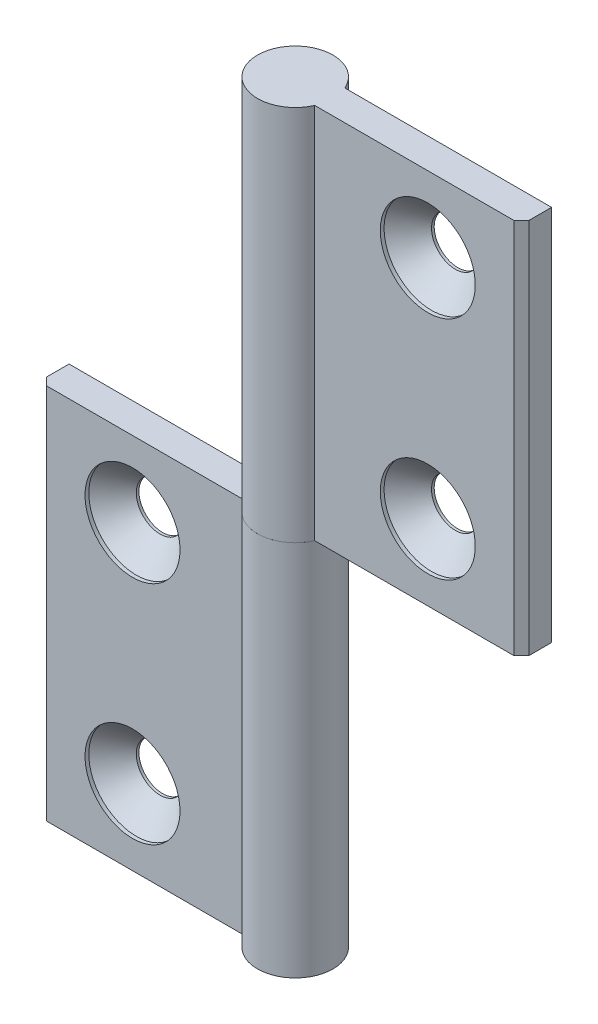
SolidWorks part; units mm, degrees
material "Алюминиевый сплав"
ref_plane "Спереди" through (0, 0, 0) normal (0, 0, 1) x (1, 0, 0)
ref_plane "Сверху" through (0, 0, 0) normal (0, 1, 0) x (1, 0, 0)
ref_plane "Справа" through (0, 0, 0) normal (1, 0, 0) x (0, 0, -1)
sketch "Эскиз1" plane through (0, 0, 0) normal (0, 1, 0) x (1, 0, 0)
  line L0 (-4.5826, 2) -> (-32, 2)
  line L1 (-32, 2) -> (-32, -1)
  line L2 (-32, -1) -> (-31, -2)
  line L3 (-31, -2) -> (-4.5826, -2)
  line L5 (-18.2913, 2) -> (-18.2913, -2) construction
  arc A0 (-4.5826, -2) -> (-4.5826, 2) centre (0, 0) ccw
  point P1 (-18.2913, 0)
  dimension "D5" = 5
  dimension "D1" = 27
  dimension "D2" = 4
  dimension "D3" = 3
  dimension "D4" = 45
extrude "Бобышка-Вытянуть1" add sketch "Эскиз1" along normal mid plane 50
hole_wizard "Зенковка для винта с полупотайной головкой M61" positions "Эскиз4" profile "Эскиз6" countersink size "M6" standard "ISO" end condition through all
sketch "Эскиз4" plane through (0, 0, 2) normal (0, 0, 1) x (1, 0, 0)
  line L0 (-19.5826, 15) -> (-19.5826, -15)
  line L2 (0.2087, -18.4577) -> (0.2087, 25) construction
  line L4 (5, 25) -> (-4.5826, 25) construction
  line L5 (-4.5826, 25) -> (-4.5826, -25) construction
  point P0 (-19.5826, 15)
  point P2 (-19.5826, -15)
  point P9 (-19.5826, 0)
  dimension "D1" = 30
  dimension "D2" = 15
sketch "Эскиз6" plane through (-19.5826, 15, 2) normal (1, 0, 0) x (0, -1, 0)
  line L0 (0, 0) -> (0, 7)
  line L1 (0, 7) -> (3.15, 7)
  line L2 (3.15, 7) -> (3.15, 3.65)
  line L3 (3.15, 3.65) -> (6.3, 0.5)
  line L4 (6.3, 0.5) -> (6.3, 0)
  line L6 (6.3, 0) -> (0, 0)
  line L7 (-3.15, 3.65) -> (-6.3, 0.5) construction
  line L11 (0, -6.35) -> (0, 107.95) construction
  dimension "Диаметр сквозного отверстия" = 6.3
  dimension "Глубина сквозного отверстия" = 7
  dimension "Диаметр зенковки" = 12.6
  dimension "Угол зенковки" = 90
  dimension "Утопленность" = 0.5
sketch "Угол раскрытия" plane through (0, 25, 0) normal (0, 1, 0) x (1, 0, 0)
  line L0 (0, 0) -> (0, -10)
  line L7 (-4.5826, 2) -> (-32, 2) construction
  dimension "D1" = 10
  dimension "D2" = 90
pattern_circular "Круговой массив1" count 2 over 360 about axis through (0, 25, 0) along (0, 0, 1) of bodies 106
